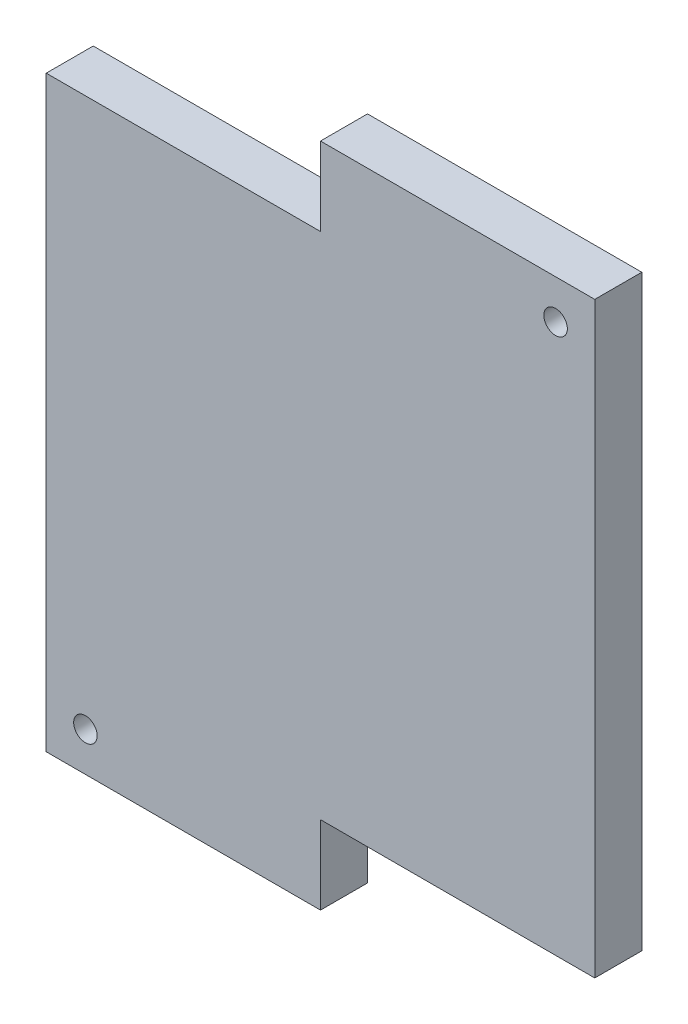
SolidWorks part; units mm, degrees
material "Acrylic (Medium-high impact)"
ref_plane "Front Plane" through (0, 0, 0) normal (0, 0, 1) x (1, 0, 0)
ref_plane "Top Plane" through (0, 0, 0) normal (0, 1, 0) x (1, 0, 0)
ref_plane "Right Plane" through (0, 0, 0) normal (1, 0, 0) x (0, 0, -1)
sketch "Sketch1" plane through (0, 0, 0) normal (0, 0, 1) x (1, 0, 0)
  line L13 (0, 0) -> (35, 0)
  line L14 (0, 0) -> (0, 75)
  line L15 (35, 85) -> (70, 85)
  line L16 (70, 10) -> (70, 85)
  line L23 (0, 75) -> (35, 75)
  line L24 (35, 85) -> (35, 75)
  line L27 (70, 10) -> (35, 10)
  line L28 (35, 0) -> (35, 10)
  circle A4 centre (65, 80) radius 1.5
  circle A5 centre (5, 5) radius 1.5
  dimension "D7" = 5
  dimension "D9" = 3
  dimension "D8" = 5
  dimension "D12" = 3
  dimension "D1" = 10
  dimension "D2" = 35
  dimension "D3" = 35
  dimension "D4" = 10
  dimension "D5" = 65
  dimension "D6" = 70
  dimension "D10" = 5
  dimension "D11" = 5
extrude "Boss-Extrude1" add sketch "Sketch1" along normal blind 6
